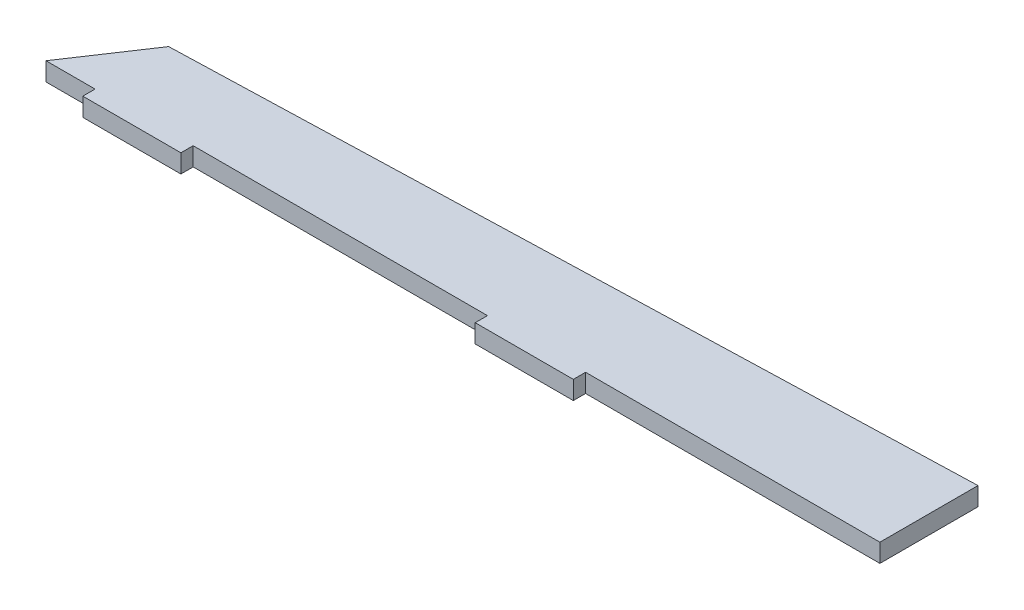
SolidWorks part; units mm, degrees
material "Plain Carbon Steel"
ref_plane "Front Plane" through (0, 0, 0) normal (0, 0, 1) x (1, 0, 0)
ref_plane "Top Plane" through (0, 0, 0) normal (0, 1, 0) x (1, 0, 0)
ref_plane "Right Plane" through (0, 0, 0) normal (1, 0, 0) x (0, 0, -1)
sketch "Sketch1" plane through (0, 0, 0) normal (0, 1, 0) x (1, 0, 0)
  line L0 (0, 0) -> (-215.9, 0)
  line L1 (-215.9, 0) -> (-203.2, 19.05)
  line L2 (-203.2, 19.05) -> (0, 25.4)
  line L3 (0, 25.4) -> (0, 0)
  dimension "D1" = 215.9
  dimension "D2" = 25.4
  dimension "D3" = 19.05
  dimension "D4" = 12.7
extrude "Boss-Extrude1" add sketch "Sketch1" along normal blind 4.7625
sketch "Sketch2" plane through (0, 4.7625, 0) normal (0, 1, 0) x (1, 0, 0)
  line L0 (-215.9, 0) -> (0, 0) construction
  line L5 (-203.2, 0) -> (-177.8, 0)
  line L6 (-203.2, 0) -> (-203.2, -3.175)
  line L7 (-203.2, -3.175) -> (-177.8, -3.175)
  line L8 (-177.8, 0) -> (-177.8, -3.175)
  line L10 (-101.6, 0) -> (-76.2, 0)
  line L11 (-101.6, 0) -> (-101.6, -3.175)
  line L12 (-101.6, -3.175) -> (-76.2, -3.175)
  line L13 (-76.2, 0) -> (-76.2, -3.175)
  dimension "D3" = 76.2
  dimension "D4" = 25.4
  dimension "D5" = 76.2
  dimension "D6" = 3.175
extrude "Boss-Extrude2" add sketch "Sketch2" against normal up to surface (4.7625 mm away) up to face at (-104.775, 0, -11.1125)
